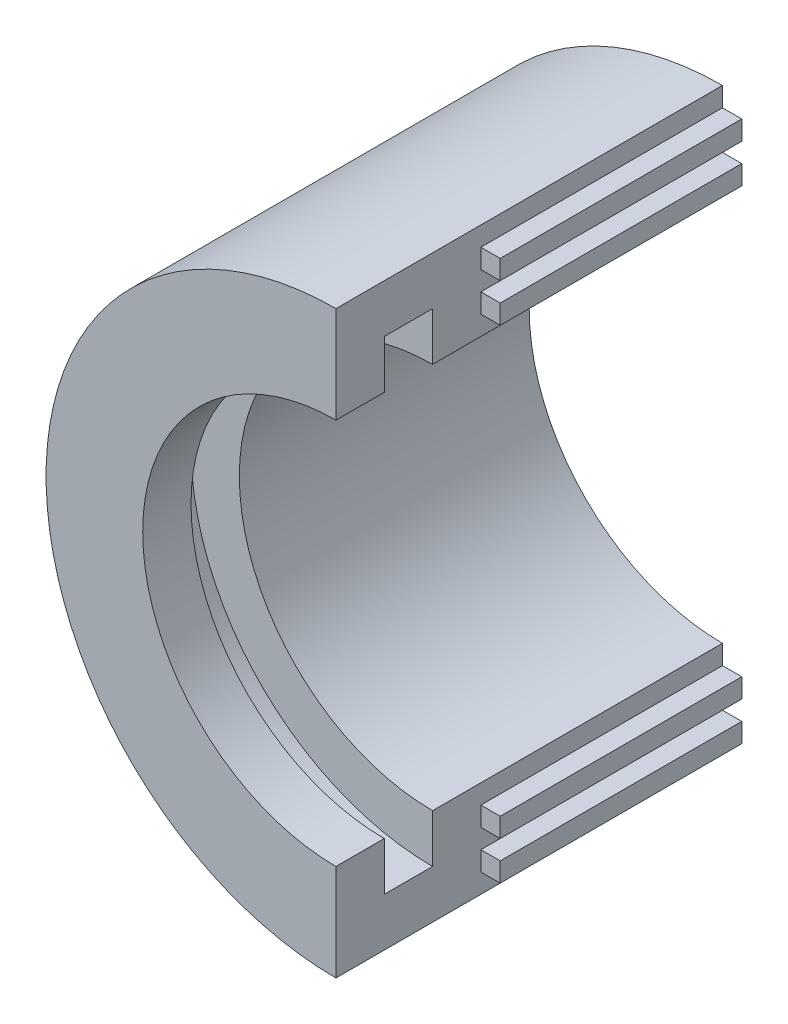
SolidWorks part; units mm, degrees
ref_plane "Front Plane" through (0, 0, 0) normal (0, 0, 1) x (1, 0, 0)
ref_plane "Top Plane" through (0, 0, 0) normal (0, 1, 0) x (1, 0, 0)
ref_plane "Right Plane" through (0, 0, 0) normal (1, 0, 0) x (0, 0, -1)
sketch "Sketch1" plane through (0, 0, 0) normal (0, 0, 1) x (1, 0, 0)
  circle A0 centre (0, 0) radius 76.2
  dimension "D1" = 152.4
extrude "Boss-Extrude1" add sketch "Sketch1" along normal blind 101.6
sketch "Sketch2" plane through (0, 0, 101.6) normal (0, 0, 1) x (1, 0, 0)
  circle A0 centre (0, 0) radius 63.5
  dimension "D1" = 127
extrude "Cut-Extrude1" cut sketch "Sketch2" against normal blind 25.4
sketch "Sketch3" plane through (0, 0, 101.6) normal (0, 0, 1) x (1, 0, 0)
  circle A0 centre (0, 0) radius 50.8
  circle A1 centre (0, 0) radius 63.5
  dimension "D1" = 127
  dimension "D2" = 101.6
extrude "Boss-Extrude2" add sketch "Sketch3" against normal blind 12.7
sketch "Sketch4" plane through (0, 0, 0) normal (0, 0, -1) x (-1, 0, 0)
  circle A0 centre (0, 0) radius 50.8
  dimension "D1" = 101.6
extrude "Cut-Extrude2" cut sketch "Sketch4" against normal through all
sketch "Sketch5" plane through (0, 0, 101.6) normal (0, 0, 1) x (1, 0, 0)
  line L0 (0, 76.2) -> (0, -76.2)
  arc A0 (0, -76.2) -> (0, 76.2) centre (0, 0) ccw
extrude "Cut-Extrude3" cut sketch "Sketch5" against normal through all
sketch "Sketch6" plane through (0, 0, 0) normal (1, 0, 0) x (0, 0, -1)
  line L0 (0, -50.8) -> (0, -76.2) construction
  line L1 (0, -55.88) -> (-63.5, -55.88)
  line L2 (0, -55.88) -> (0, -60.96)
  line L3 (0, -60.96) -> (-63.5, -60.96)
  line L4 (-63.5, -55.88) -> (-63.5, -60.96)
  line L5 (-76.2, -50.8) -> (0, -50.8) construction
  dimension "D1" = 5.08
  dimension "D2" = 5.08
  dimension "D3" = 63.5
extrude "Boss-Extrude4" add sketch "Sketch6" along normal blind 5.08
pattern_linear "LPattern1" count 2 spacing 10.16 along (0, -1, 0) of "Boss-Extrude4"
ref_plane "Plane1" through (0, 0, 0) normal (0, 1, 0) x (1, 0, 0)
mirror "Mirror1" about plane through (0, 0, 0) normal (0, 1, 0) of "LPattern1", "Boss-Extrude4"
